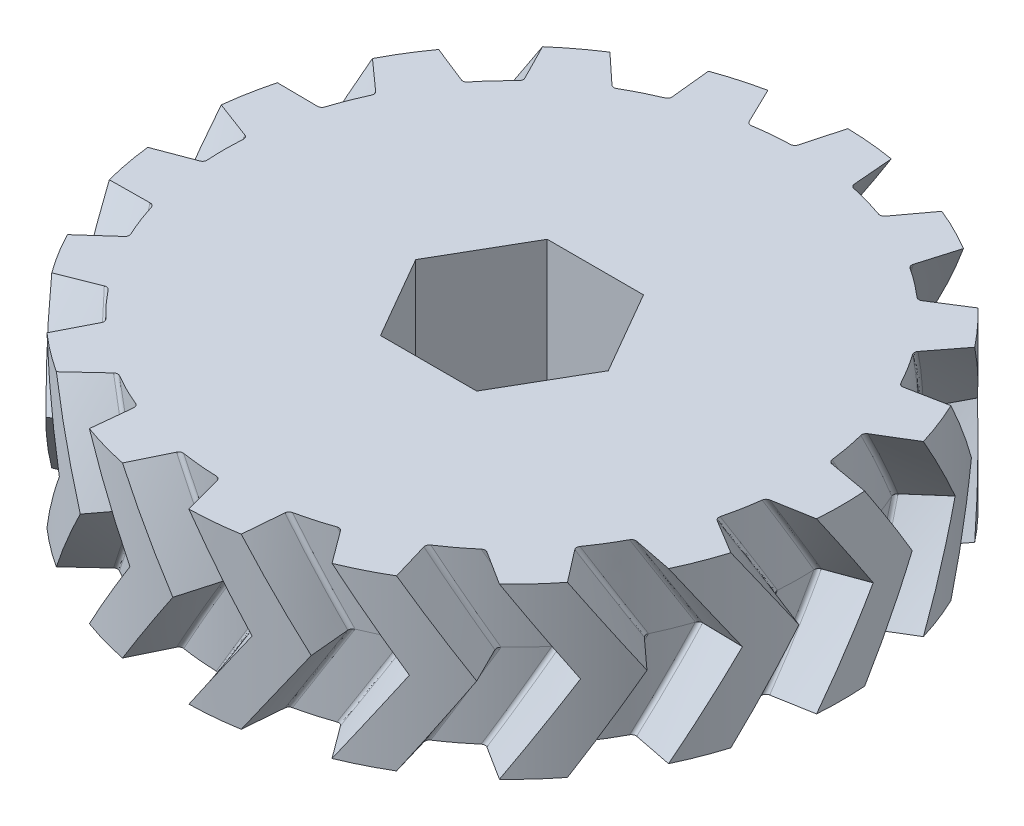
SolidWorks part; units mm, degrees
ref_plane "Front Plane" through (0, 0, 0) normal (0, 0, 1) x (1, 0, 0)
ref_plane "Top Plane" through (0, 0, 0) normal (0, 1, 0) x (1, 0, 0)
ref_plane "Right Plane" through (0, 0, 0) normal (1, 0, 0) x (0, 0, -1)
sketch "Sketch1" plane through (0, 0, 0) normal (0, 1, 0) x (1, 0, 0)
  line L1 (4.2724, 0) -> (2.1362, 3.7)
  line L2 (2.1362, 3.7) -> (-2.1362, 3.7)
  line L3 (-2.1362, 3.7) -> (-4.2724, 0)
  line L4 (-4.2724, 0) -> (-2.1362, -3.7)
  line L5 (-2.1362, -3.7) -> (2.1362, -3.7)
  line L6 (2.1362, -3.7) -> (4.2724, 0)
  circle A0 centre (0, 0) radius 13.5 construction
  circle A1 centre (0, 0) radius 14.625
  circle A2 centre (0, 0) radius 3.7 construction
  dimension "D1" = 29.25
  dimension "D2" = 27
  dimension "D3" = 7.4
extrude "Boss-Extrude1" add sketch "Sketch1" along normal blind 3.75 contours A0 L6 L5 L4 L3 L2 L1
sketch "Sketch2" plane through (0, 3.75, 0) normal (0, 1, 0) x (1, 0, 0)
  line L0 (0, 13.5) -> (0, 0) construction
  line L1 (-0.2, 13) -> (0.2, 13)
  arc A0 (0, 15.1515) -> (-0.7, 14.6082) centre (0.2043, 14.1657) ccw
  circle A2 centre (0, 0) radius 14.625 construction
  arc A3 (0.4, 13.2279) -> (0.7, 14.6082) centre (29.8575, 7.5484) cw
  arc A5 (0, 15.1515) -> (0.7, 14.6082) centre (-0.2043, 14.1657) cw
  arc A7 (0.4, 13.2279) -> (0.2, 13) centre (0.1054, 13.2847) cw
  arc A8 (-0.4, 13.2279) -> (-0.2, 13) centre (-0.1054, 13.2847) ccw
  arc A9 (-0.4, 13.2279) -> (-0.7, 14.6082) centre (-29.8575, 7.5484) ccw
  point P13 (0, 13)
  point P14 (0.0153, 13.5)
  point P18 (0, 13)
  point P19 (-0.5, 13.5)
  point P22 (0.4, 13.2279)
  dimension "D1" = 0.2
  dimension "D3" = 30
  dimension "D5" = 13
  dimension "D6" = 0.3
  dimension "D2" = 0.2
  dimension "D4" = 0.3
ref_plane "Plane2" through (0, 0, 3.7) normal (0, 0, -1) x (1, 0, 0)
sketch "Sketch4" plane through (0, 0, 3.7) normal (0, 0, -1) x (1, 0, 0)
  line L0 (0, 0) -> (0, -7.5)
  circle A0 centre (0, -3.75) radius 2.25
  dimension "D2" = 4.5
  dimension "D1" = 7.5
sketch "Sketch6" plane through (0, 0, 0) normal (0, -1, 0) x (1, 0, 0)
  circle A0 centre (0, 0) radius 14.25
curve "Helix/Spiral1" pitch 135 height 3.753 turns 0.0278
sketch "Sketch10" plane through (0, 0, 0) normal (0, -1, 0) x (1, 0, 0)
  line L0 (0, 0) -> (-9.7695, 0) construction
  line L1 (-12.8541, 0.9983) -> (-14.5614, 1.6408)
  line L2 (-15.0253, 2.0539) -> (-15.0253, -2.0539)
  line L4 (-12.8541, -0.9983) -> (-14.5614, -1.6408)
  circle A0 centre (0, 0) radius 12.75 construction
  arc A1 (-14.5614, 1.6408) -> (-15.0253, 2.0539) centre (-14.4474, 2.2359) cw
  arc A3 (-12.725, -0.7986) -> (-12.725, 0.7986) centre (0, 0) cw
  arc A5 (-14.5614, -1.6408) -> (-15.0253, -2.0539) centre (-14.4474, -2.2359) ccw
  arc A6 (-12.725, -0.7986) -> (-12.8541, -0.9983) centre (-12.9246, -0.8111) cw
  arc A7 (-12.725, 0.7986) -> (-12.8541, 0.9983) centre (-12.9246, 0.8111) ccw
  point P20 (-13.7789, 0)
  point P22 (-12.7149, -0.9459)
  point P25 (-12.7149, 0.9459)
  point P39 (-15.0253, 0)
  dimension "D1" = 25.5
  dimension "D2" = 0.2
  dimension "D3" = 0.2
sweep "Cut-Sweep2" cut profiles "Sketch10" path "Helix/Spiral1"
pattern_circular "CirPattern1" count 17 over 360 about axis through (0, 3.75, 0) along (0, 1, 0) of "Cut-Sweep2"
mirror "Mirror2" about plane through (0, 3.75, 0) normal (0, 1, 0) of "Boss-Extrude1", "Cut-Sweep2", "CirPattern1"
